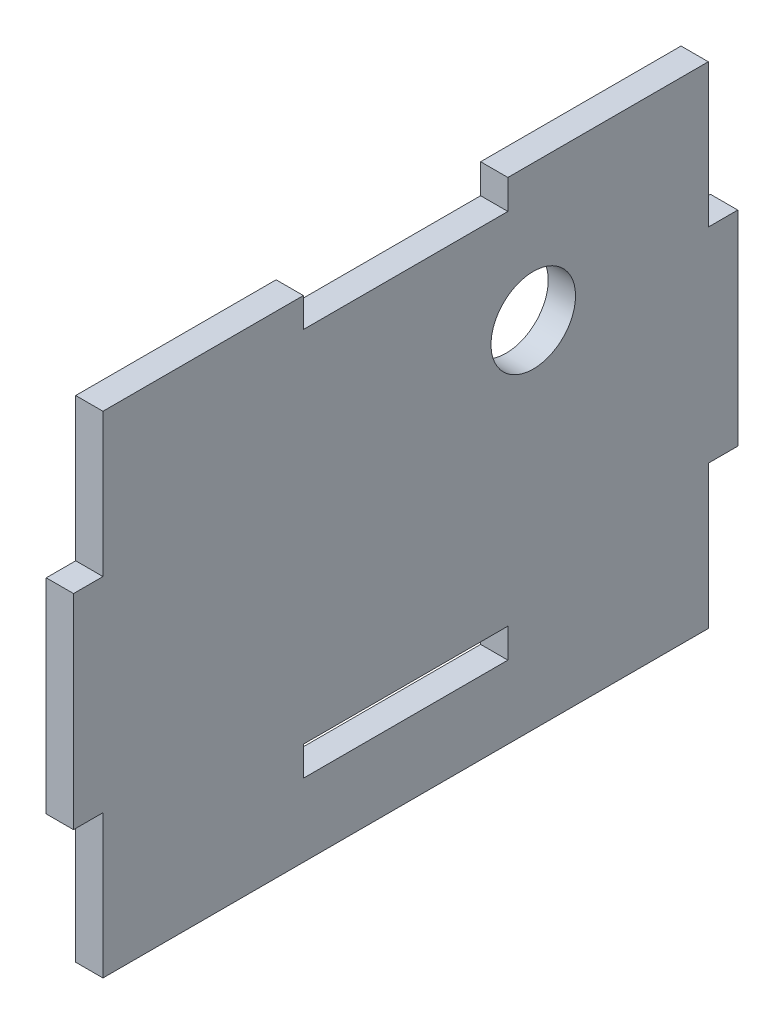
SolidWorks part; units mm, degrees
ref_plane "Front Plane" through (0, 0, 0) normal (0, 0, 1) x (1, 0, 0)
ref_plane "Top Plane" through (0, 0, 0) normal (0, 1, 0) x (1, 0, 0)
ref_plane "Right Plane" through (0, 0, 0) normal (1, 0, 0) x (0, 0, -1)
sketch "Sketch1" plane through (0, 0, 0) normal (1, 0, 0) x (0, 0, -1)
  line L1 (28.194, -22.86) -> (-28.194, -22.86)
  line L2 (28.194, -22.86) -> (28.194, 22.86)
  line L3 (28.194, 22.86) -> (-28.194, 22.86)
  line L4 (-28.194, -22.86) -> (-28.194, 22.86)
  line L5 (28.194, -22.86) -> (-28.194, 22.86) construction
  line L6 (28.194, 22.86) -> (-28.194, -22.86) construction
  point P0 (0, 0)
  dimension "D1" = 56.388
  dimension "D2" = 45.72
extrude "Boss-Extrude1" add sketch "Sketch1" along normal blind 2.54
sketch "Sketch2" plane through (2.54, 0, 0) normal (1, 0, 0) x (0, 0, -1)
  line L0 (-28.194, 22.86) -> (-28.194, -22.86) construction
  line L1 (-30.9372, 9.525) -> (-28.194, 9.525)
  line L2 (-30.9372, 9.525) -> (-30.9372, -9.525)
  line L3 (-30.9372, -9.525) -> (-28.194, -9.525)
  line L4 (-28.194, 9.525) -> (-28.194, -9.525)
  line L5 (-30.9372, 9.525) -> (-28.194, -9.525) construction
  line L6 (-30.9372, -9.525) -> (-28.194, 9.525) construction
  line L7 (28.194, -22.86) -> (28.194, 22.86) construction
  line L8 (30.9372, 9.525) -> (28.194, 9.525)
  line L9 (30.9372, 9.525) -> (30.9372, -9.525)
  line L10 (30.9372, -9.525) -> (28.194, -9.525)
  line L11 (28.194, 9.525) -> (28.194, -9.525)
  line L12 (30.9372, 9.525) -> (28.194, -9.525) construction
  line L13 (30.9372, -9.525) -> (28.194, 9.525) construction
  line L14 (-29.5656, 0) -> (29.5656, 0) construction
  point P0 (-29.5656, 0)
  point P7 (29.5656, 0)
  dimension "D1" = 19.05
  dimension "D2" = 2.7432
extrude "Boss-Extrude2" add sketch "Sketch2" against normal up to surface (2.54 mm away) up to face at (0, 0, 0)
sketch "Sketch3" plane through (2.54, 0, 0) normal (1, 0, 0) x (0, 0, -1)
  line L0 (28.194, 22.86) -> (-28.194, 22.86) construction
  line L1 (-9.525, 20.1168) -> (9.525, 20.1168)
  line L2 (-9.525, 20.1168) -> (-9.525, 22.86)
  line L3 (-9.525, 22.86) -> (9.525, 22.86)
  line L4 (9.525, 20.1168) -> (9.525, 22.86)
  line L5 (-9.525, 20.1168) -> (9.525, 22.86) construction
  line L6 (-9.525, 22.86) -> (9.525, 20.1168) construction
  line L7 (-28.194, -22.86) -> (28.194, -22.86) construction
  line L8 (9.525, -13.335) -> (-9.525, -13.335)
  line L9 (9.525, -13.335) -> (9.525, -16.0782)
  line L10 (9.525, -16.0782) -> (-9.525, -16.0782)
  line L11 (-9.525, -13.335) -> (-9.525, -16.0782)
  line L12 (9.525, -13.335) -> (-9.525, -16.0782) construction
  line L13 (9.525, -16.0782) -> (-9.525, -13.335) construction
  line L14 (0, -14.7066) -> (0, 21.4884) construction
  point P0 (0, 21.4884)
  point P7 (0, -14.7066)
  dimension "D1" = 19.05
  dimension "D2" = 9.525
  dimension "D3" = 2.7432
extrude "Cut-Extrude1" cut sketch "Sketch3" against normal through all
sketch "Sketch4" plane through (2.54, 0, 0) normal (1, 0, 0) x (0, 0, -1)
  line L0 (28.194, 22.86) -> (9.525, 22.86) construction
  line L2 (30.9372, -9.525) -> (30.9372, 9.525) construction
  circle A0 centre (11.8872, 10.16) radius 3.937
  point P6 (30.9372, 5.4541)
  dimension "D1" = 7.874
  dimension "D2" = 12.7
  dimension "D3" = 19.05
extrude "Cut-Extrude2" cut sketch "Sketch4" against normal through all
